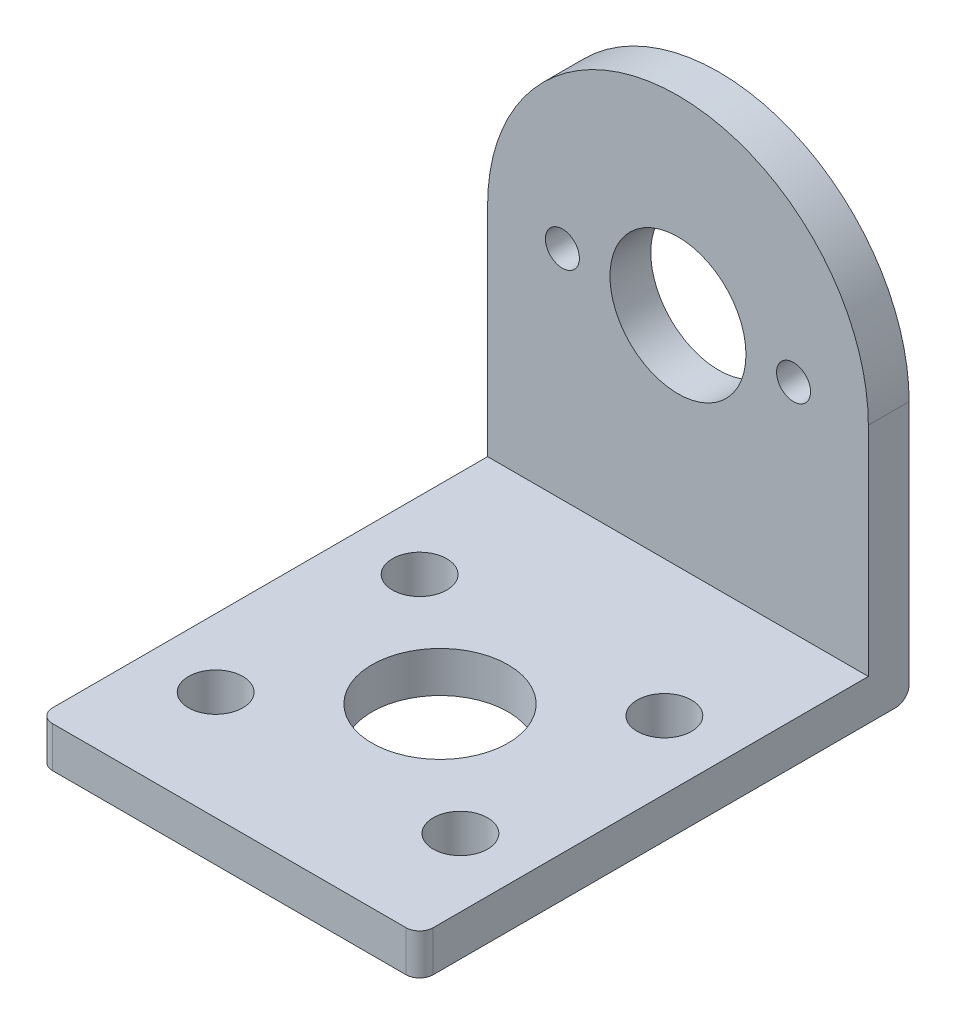
SolidWorks part; units mm, degrees
ref_plane "Front Plane" through (0, 0, 0) normal (0, 0, 1) x (1, 0, 0)
ref_plane "Top Plane" through (0, 0, 0) normal (0, 1, 0) x (1, 0, 0)
ref_plane "Right Plane" through (0, 0, 0) normal (1, 0, 0) x (0, 0, -1)
sketch "Sketch1" plane through (0, 0, 0) normal (0, 0, 1) x (1, 0, 0)
  line L0 (0, 0) -> (-8.5, 0) construction
  line L1 (0, 0) -> (8.5, 0) construction
  line L2 (-14, 0) -> (-14, -19)
  line L3 (14, 0) -> (14, -19)
  line L4 (14, -19) -> (-14, -19)
  arc A0 (14, 0) -> (-14, 0) centre (0, 0) ccw
  circle A1 centre (0, 0) radius 5
  circle A2 centre (-8.5, 0) radius 1.25
  circle A3 centre (8.5, 0) radius 1.25
  dimension "D1" = 28
  dimension "D2" = 10
  dimension "D3" = 2.5
  dimension "D5" = 2.5
  dimension "D4" = 8.5
  dimension "D6" = 8.5
  dimension "D7" = 19
extrude "Boss-Extrude1" add sketch "Sketch1" along normal blind 3
sketch "Sketch2" plane through (0, 0, 3) normal (0, 0, 1) x (1, 0, 0)
  line L0 (14, -19) -> (14, 0) construction
  line L1 (-14, -19) -> (14, -19)
  line L2 (-14, -19) -> (-14, -16)
  line L3 (-14, -16) -> (14, -16)
  line L4 (14, -19) -> (14, -16)
  dimension "D1" = 3
extrude "Boss-Extrude2" add sketch "Sketch2" along normal blind 33
fillet "Fillet1" radius 1 3 edges at (14, -17.5, 36) (-14, -17.5, 36) (0, -19, 0)
sketch "Sketch4" plane through (0, -19, 0) normal (0, -1, 0) x (1, 0, 0)
  line L0 (-9, 36) -> (-9, 0) construction
  line L1 (-13, 36) -> (13, 36) construction
  line L2 (14, 0) -> (-14, 0) construction
  line L3 (-14, 35) -> (-14, 1) construction
  line L4 (-9, 28) -> (14, 28) construction
  line L5 (14, 35) -> (14, 1) construction
  line L6 (0, 36) -> (0, 0) construction
  line L7 (9, 28) -> (9, 0) construction
  line L9 (-9, 13) -> (9, 28) construction
  circle A0 centre (-9, 28) radius 2
  circle A1 centre (-9, 13) radius 2
  circle A2 centre (9, 28) radius 2
  circle A3 centre (9, 13) radius 2
  circle A4 centre (0, 20.5) radius 5
  dimension "D3" = 4
  dimension "D4" = 4
  dimension "D7" = 4
  dimension "D8" = 4
  dimension "D10" = 10
  dimension "D1" = 5
  dimension "D2" = 8
  dimension "D5" = 15
  dimension "D6" = 5
  dimension "D9" = 15
extrude "Cut-Extrude1" cut sketch "Sketch4" against normal blind 10
